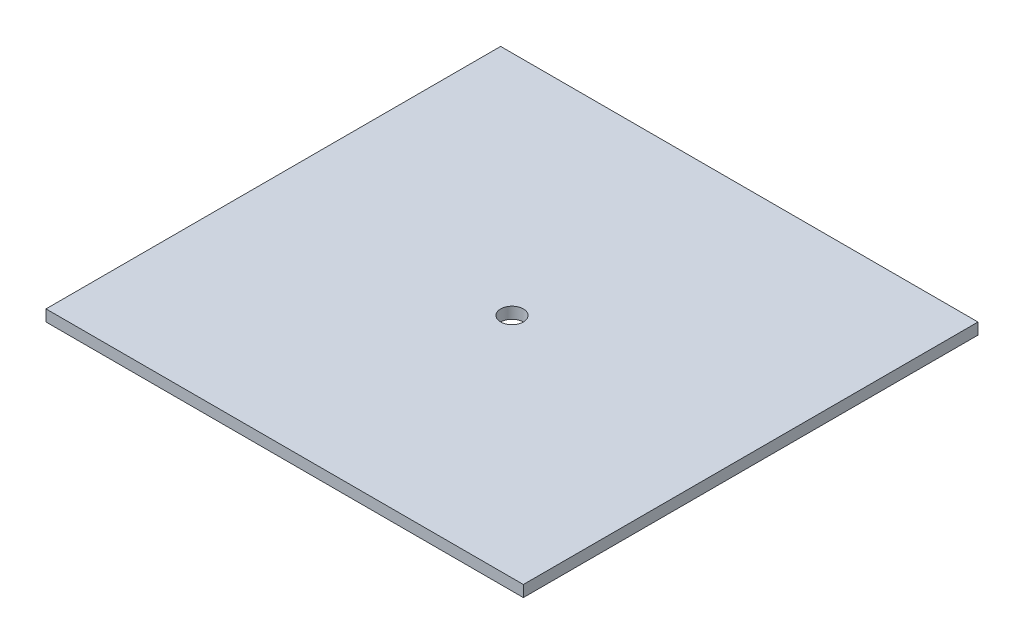
SolidWorks part; units mm, degrees
ref_plane "Front Plane" through (0, 0, 0) normal (0, 0, 1) x (1, 0, 0)
ref_plane "Top Plane" through (0, 0, 0) normal (0, 1, 0) x (1, 0, 0)
ref_plane "Right Plane" through (0, 0, 0) normal (1, 0, 0) x (0, 0, -1)
sketch "Sketch1" plane through (0, 0, 0) normal (0, 1, 0) x (1, 0, 0)
  line L1 (66.675, -63.5) -> (-66.675, -63.5)
  line L2 (66.675, -63.5) -> (66.675, 63.5)
  line L3 (66.675, 63.5) -> (-66.675, 63.5)
  line L4 (-66.675, -63.5) -> (-66.675, 63.5)
  line L5 (66.675, -63.5) -> (-66.675, 63.5) construction
  line L6 (66.675, 63.5) -> (-66.675, -63.5) construction
  point P0 (0, 0)
  dimension "D1" = 133.35
  dimension "D2" = 127
extrude "Boss-Extrude1" add sketch "Sketch1" along normal blind 3.175
sketch "Sketch2" plane through (0, 3.175, 0) normal (0, 1, 0) x (1, 0, 0)
  circle A0 centre (0, 0) radius 3.175
  dimension "D1" = 6.35
extrude "Cut-Extrude1" cut sketch "Sketch2" against normal through all
